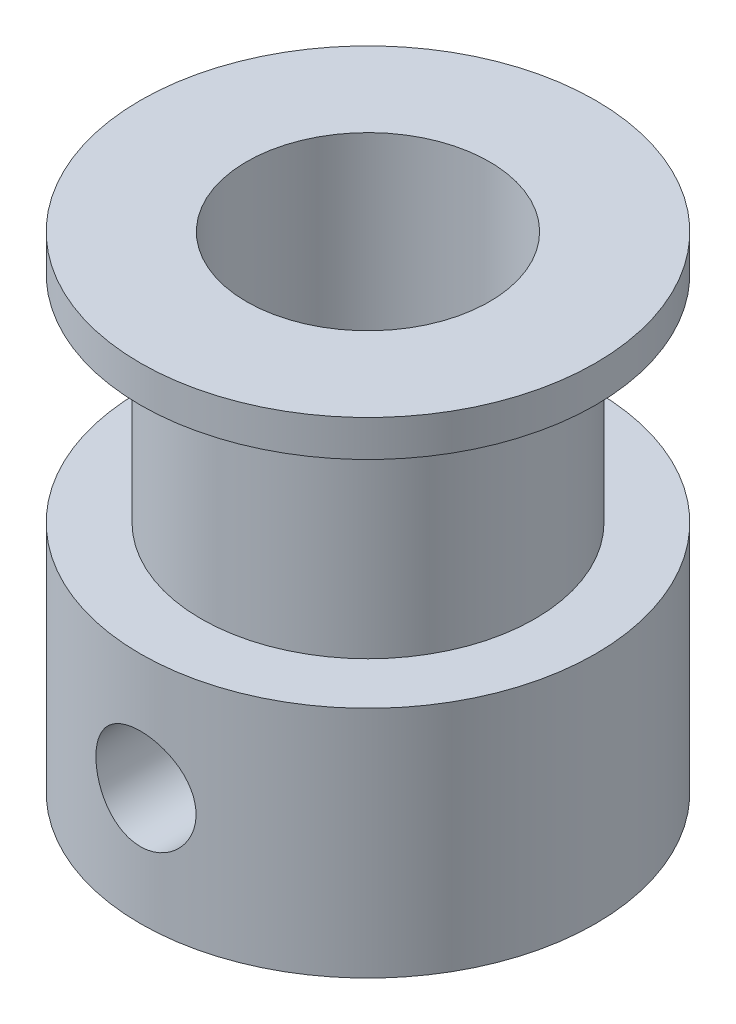
SolidWorks part; units mm, degrees
material "aluminio"
ref_plane "Alzado" through (0, 0, 0) normal (0, 0, 1) x (1, 0, 0)
ref_plane "Planta" through (0, 0, 0) normal (0, 1, 0) x (1, 0, 0)
ref_plane "Vista lateral" through (0, 0, 0) normal (1, 0, 0) x (0, 0, -1)
sketch "Croquis1" plane through (0, 0, 0) normal (0, 1, 0) x (1, 0, 0)
  circle A0 centre (0, 0) radius 7.5
  dimension "D1" = 15
extrude "Saliente-Extruir1" add sketch "Croquis1" along normal blind 7.7
sketch "Croquis2" plane through (0, 7.7, 0) normal (0, 1, 0) x (1, 0, 0)
  circle A0 centre (0, 0) radius 5.5
  dimension "D1" = 11
extrude "Saliente-Extruir2" add sketch "Croquis2" along normal blind 7.1
sketch "Croquis3" plane through (0, 14.8, 0) normal (0, 1, 0) x (1, 0, 0)
  circle A0 centre (0, 0) radius 7.5
  circle A1 centre (0, 0) radius 7.5 construction
extrude "Saliente-Extruir3" add sketch "Croquis3" along normal blind 1.2
sketch "Croquis4" plane through (0, 16, 0) normal (0, 1, 0) x (1, 0, 0)
  circle A0 centre (0, 0) radius 4
  dimension "D1" = 8
extrude "Cortar-Extruir1" cut sketch "Croquis4" against normal through all
hole_wizard "Taladro roscado M31 (definir posicio)" positions "Croquis6" profile "Croquis5" tap size "M4" standard "ISO"
sketch "Croquis6" plane through (0, 0, 0) normal (0, 0, 1) x (1, 0, 0)
  line L0 (0, 7.7) -> (0, 0) construction
  line L1 (7.5, 7.7) -> (-7.5, 7.7) construction
  point P0 (0, 3.85)
sketch "Croquis5" plane through (0, 3.85, 0) normal (1, 0, 0) x (0, 1, 0)
  line L0 (0, 0) -> (0, 7.501)
  line L1 (0, 7.501) -> (1.65, 7.501)
  line L2 (1.65, 7.501) -> (1.65, 0)
  line L5 (1.65, 0) -> (0, 0)
  line L11 (0, -6.35) -> (0, 107.95) construction
  dimension "Diámetro de perforador para roscar hasta el siguiente" = 3.3
  dimension "Profundidad de perforador para roscar hasta el siguiente" = 7.501
cosmetic thread "Rosca de taladro1" parameters "D2"=4
pattern_circular "MatrizC1" count 2 every 90 about axis through (0, 7.7, 0) along (0, -1, 0) of "Taladro roscado M31 (definir posicio)"
cosmetic thread "Rosca cosmética2" parameters "D2"=3.6
